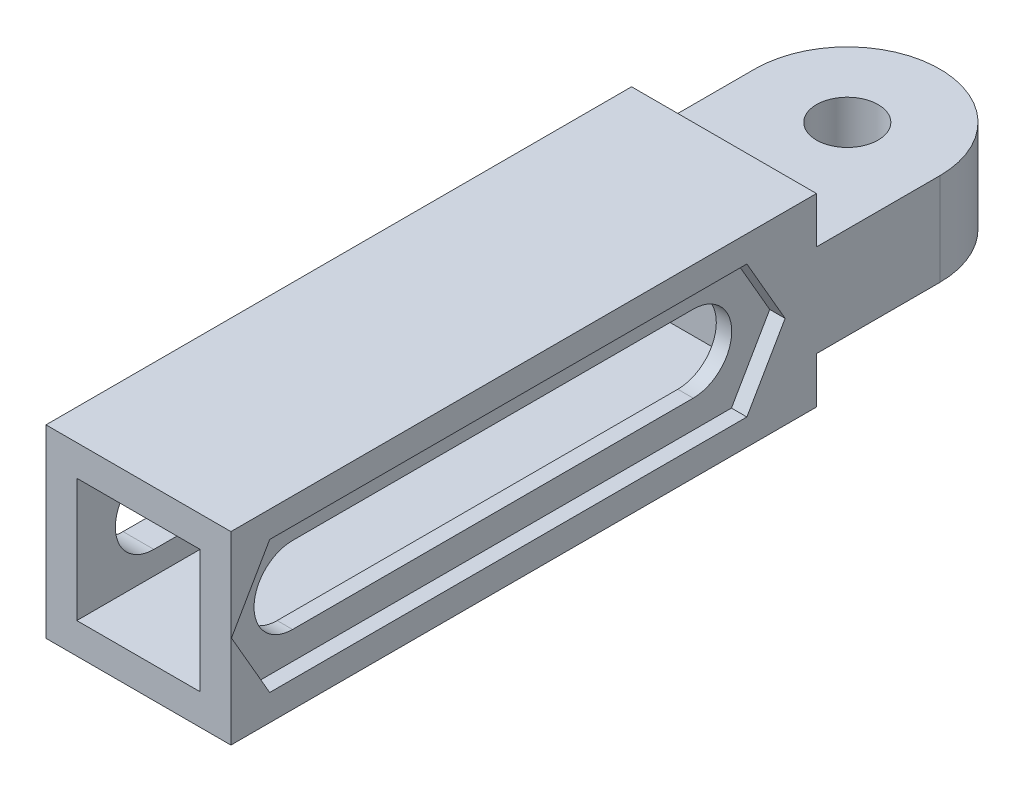
SolidWorks part; units mm, degrees
ref_plane "정면" through (0, 0, 0) normal (0, 0, 1) x (1, 0, 0)
ref_plane "윗면" through (0, 0, 0) normal (0, 1, 0) x (1, 0, 0)
ref_plane "우측면" through (0, 0, 0) normal (1, 0, 0) x (0, 0, -1)
sketch "스케치1" plane through (0, 0, 0) normal (0, 0, 1) x (1, 0, 0)
  line L1 (3, 3) -> (-3, 3)
  line L2 (3, 3) -> (3, -3)
  line L3 (3, -3) -> (-3, -3)
  line L4 (-3, 3) -> (-3, -3)
  line L5 (2, 2) -> (-2, 2)
  line L6 (2, 2) -> (2, -2)
  line L7 (2, -2) -> (-2, -2)
  line L8 (-2, 2) -> (-2, -2)
  point P4 (0, 3)
  point P5 (3, 0)
  point P11 (2, 0)
  point P12 (0, 2)
  dimension "D1" = 6
  dimension "D2" = 6
  dimension "D3" = 1
  dimension "D4" = 1
extrude "보스-돌출1" add sketch "스케치1" along normal blind 18
sketch "스케치2" plane through (0, 0, 0) normal (0, 0, -1) x (-1, 0, 0)
  line L1 (3, 3) -> (-3, 3)
  line L2 (3, 3) -> (3, -3)
  line L3 (3, -3) -> (-3, -3)
  line L4 (-3, 3) -> (-3, -3)
extrude "보스-돌출2" add sketch "스케치2" along normal blind 1
sketch "스케치3" plane through (0, 0, 0) normal (0, 1, 0) x (1, 0, 0)
  line L0 (-3, -18) -> (-3, 1) construction
  line L2 (3, 5) -> (3, 1)
  line L3 (3, 1) -> (-3, 1)
  line L4 (-3, 5) -> (-3, 1)
  line L5 (3, -18) -> (3, 1) construction
  line L6 (-3, 1) -> (3, 1) construction
  arc A0 (3, 5) -> (-3, 5) centre (0, 5) ccw
  circle A1 centre (0, 5) radius 1
  dimension "D2" = 2
  dimension "D1" = 4
extrude "보스-돌출3" add sketch "스케치3" along normal blind 1.5 and the other way blind 1.5
sketch "스케치4" plane through (-3, 0, 0) normal (-1, 0, 0) x (0, 0, 1)
  line L1 (15.5, 1.25) -> (2.5, 1.25)
  line L2 (18, 3) -> (18, -3) construction
  line L3 (15.5, -1.25) -> (2.5, -1.25)
  line L4 (-1, 1.5) -> (-1, 3) construction
  arc A0 (2.5, 1.25) -> (2.5, -1.25) centre (2.5, 0) ccw
  arc A1 (15.5, -1.25) -> (15.5, 1.25) centre (15.5, 0) ccw
  point P9 (0, 0)
  point P10 (18, 0)
  dimension "D3" = 1.25
  dimension "D1" = 2.5
  dimension "D2" = 3.5
extrude "컷-돌출1" cut sketch "스케치4" against normal up to surface (6 mm away) up to face at (3, 0, 2.75)
sketch "스케치5" plane through (3, 0, 0) normal (1, 0, 0) x (0, 0, -1)
  line L2 (-9, 2.15) -> (-16.7413, 2.15)
  line L3 (-16.7413, 2.15) -> (-17.9826, 0)
  line L4 (-17.9826, 0) -> (-16.7413, -2.15)
  line L5 (-16.7413, -2.15) -> (-9, -2.15)
  line L7 (-0.0174, 0) -> (-1.2587, 2.15)
  line L8 (-1.2587, 2.15) -> (-9, 2.15)
  line L11 (-9, -2.15) -> (-1.2587, -2.15)
  line L12 (-1.2587, -2.15) -> (-0.0174, 0)
  line L15 (-13.0174, 0) -> (-13.638, 1.075) [skipped]
  line L16 (-14.2587, -2.15) -> (-13.638, -1.075) [skipped]
  line L17 (-4.362, 1.075) -> (-4.9826, 0) [skipped]
  line L18 (-4.362, -1.075) -> (-3.7413, -2.15) [skipped]
  arc A0 (-15.5, 2.15) -> (-15.5, -2.15) centre (-15.5, 0) ccw construction
  arc A1 (-2.5, -2.15) -> (-2.5, 2.15) centre (-2.5, 0) ccw construction
  arc A2 (-2.5, -1.25) -> (-2.5, 1.25) centre (-2.5, 0) ccw construction
  point P13 (0, 0)
  point P14 (-7.4924, 2.15)
  point P15 (-1.2587, 2.15)
  point P17 (-8.033, 2.15)
  point P22 (0, 0)
  point P23 (-9, -2.15)
  point P24 (0, 0)
  point P33 (0, 0)
  dimension "D1" = 4.3
extrude "컷-돌출2" cut sketch "스케치5" against normal blind 0.5
